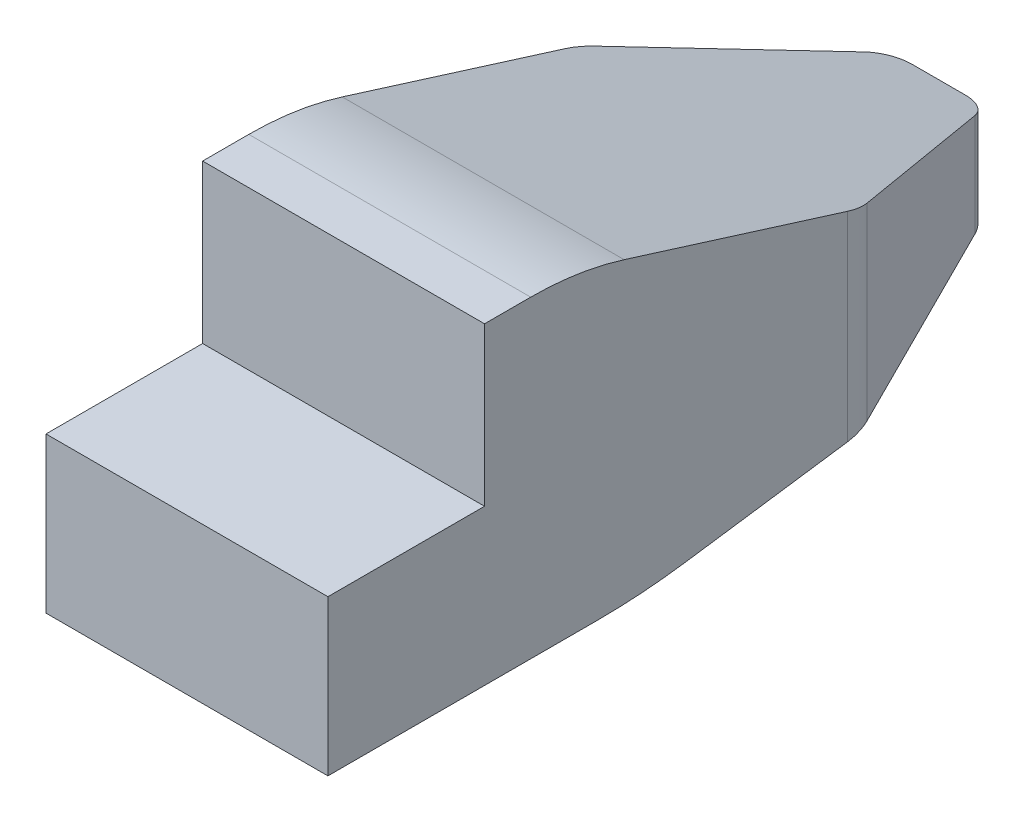
SolidWorks part; units mm, degrees
material "ﾒﾗﾐﾝ樹脂"
ref_plane "正面" through (0, 0, 0) normal (0, 0, 1) x (1, 0, 0)
ref_plane "平面" through (0, 0, 0) normal (0, 1, 0) x (1, 0, 0)
ref_plane "右側面" through (0, 0, 0) normal (1, 0, 0) x (0, 0, -1)
sketch "ｽｹｯﾁ1" plane through (0, 0, 0) normal (0, 1, 0) x (1, 0, 0)
  line L0 (0, 0) -> (9, 0)
  line L1 (9, 0) -> (9, 24)
  line L2 (9, 24) -> (0, 24)
  line L3 (0, 24) -> (0, 0)
extrude "ﾎﾞｽ - 押し出し1" add sketch "ｽｹｯﾁ1" along normal blind 10
sketch "ｽｹｯﾁ2" plane through (0, 10, 0) normal (0, 1, 0) x (1, 0, 0)
  line L0 (9, 0) -> (9, 5)
  line L1 (9, 5) -> (0, 5)
  line L2 (0, 24) -> (0, 0) construction
  line L3 (0, 5) -> (0, 0)
  line L4 (0, 0) -> (9, 0)
extrude "ｶｯﾄ - 押し出し1" cut sketch "ｽｹｯﾁ2" against normal blind 5.045
sketch "ｽｹｯﾁ3" plane through (9, 0, 0) normal (1, 0, 0) x (0, 0, -1)
  line L0 (0, 0) -> (10, 0)
  line L1 (0, 0) -> (24, 0) construction
  line L2 (24, 0) -> (24, 2)
  line L3 (24, 10) -> (24, 0) construction
  line L4 (24, 2) -> (24, 5)
  line L5 (24, 2) -> (10, 0)
  line L6 (5, 10) -> (8, 10)
  line L7 (5, 10) -> (24, 10) construction
  line L8 (8, 10) -> (24, 5)
  line M1 (24, 10) -> (5, 10)
  line M5 (0, 0) -> (24, 0)
  line M6 (24, 0) -> (24, 10)
extrude "ｶｯﾄ - 押し出し2" cut sketch "ｽｹｯﾁ3" against normal through all contours L8 M1 M6 | L5 M6 M5
sketch "ｽｹｯﾁ6" plane through (0, 0, 0) normal (0, -1, 0) x (1, 0, 0)
  line L0 (0, -10) -> (0, -17)
  line L1 (9, -10) -> (9, -17)
  line L2 (9, -17) -> (0, -17)
  line L4 (4.5, -17) -> (4.5, -24)
  line L5 (4.5, -24) -> (6, -24)
  line L6 (6, -24) -> (3, -24)
  line L7 (3, -24) -> (0, -17)
  line L8 (6, -24) -> (9, -17)
  line L9 (9, -17) -> (9, -24)
  line L10 (9, -24) -> (0, -24)
  line L11 (0, -24) -> (0, -17)
extrude "ｶｯﾄ - 押し出し4" cut sketch "ｽｹｯﾁ6" against normal through all contours L10 L9 L8 | L11 L10 L7
fillet "ﾌｨﾚｯﾄ1" radius 20 1 edges at (4.5, 0, -10)
fillet "ﾌｨﾚｯﾄ2" radius 1 2 edges at (6, 3.5, -24) (3, 3.5, -24)
fillet "ﾌｨﾚｯﾄ3" radius 2 2 edges at (9, 4.0938, -17) (0, 4.0938, -17)
fillet "ﾌｨﾚｯﾄ4" radius 10 1 edges at (4.5, 10, -8)
